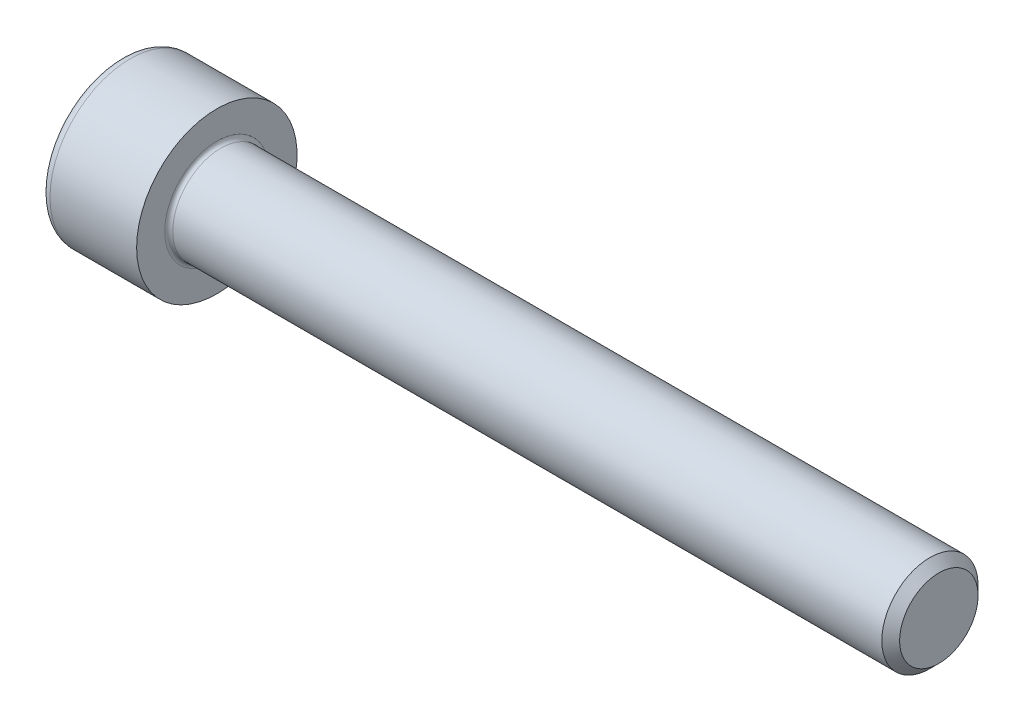
SolidWorks part; units mm, degrees
ref_plane "Plane1" through (0, 0, 0) normal (0, 0, 1) x (1, 0, 0)
ref_plane "Plane2" through (0, 0, 0) normal (0, 1, 0) x (1, 0, 0)
ref_plane "Plane3" through (0, 0, 0) normal (1, 0, 0) x (0, 0, -1)
sketch "BodySke" plane through (0, 0, 0) normal (0, 0, 1) x (1, 0, 0)
  line L0 (0, 0) -> (0, 5)
  line L1 (0, 5) -> (6, 5)
  line L2 (6, 5) -> (6, 3)
  line L3 (6, 3) -> (50.4455, 3)
  line L4 (51, 2.4455) -> (51, 0)
  line L5 (51, 0) -> (0, 0)
  line L6 (-31.75, 0) -> (127, 0) construction
  line L8 (51, 2.4455) -> (50.4455, 3)
  line L10 (51, -2.4455) -> (50.4455, -3) construction
  line L11 (7, 9.525) -> (7, 3.175) construction
  line L12 (27, 9.525) -> (27, 3.175) construction
  line L13 (-9, 9.525) -> (-9, 3.175) construction
  dimension "Diameter" = 6
  dimension "Head_ht" = 6
  dimension "Length" = 45
  dimension "Body_ch_ang" = 45
  dimension "Head_dia" = 10
  dimension "Minor_dia" = 4.891
  dimension "Advance" = 1
  dimension "Thread_nom" = 24
  dimension "Thread_length" = 60
revolve "Base-Revolve" add sketch "BodySke"
cosmetic thread "ThreadCosmetic" [suppressed]
fillet "Fillet1" radius 0.25 1 edges at (6, 0, 3)
fillet "Fillet2" radius 0.6 1 edges at (0, 0, 5)
sketch "Sketch2" plane through (0, 0, 0) normal (0, 0, 1) x (1, 0, 0)
  line L0 (0, 2.51) -> (3, 2.51)
  line L1 (3, 2.51) -> (4.4491, 0)
  line L2 (-31.75, 0) -> (127, 0) construction
  line L3 (4.4491, 0) -> (0, 0)
  line L4 (0, 0) -> (0, 2.51)
  line L6 (0, 0) -> (47.625, 0) construction
  dimension "D1" = 2.51
  dimension "D2" = 60
  dimension "Depth" = 3
revolve "Hex-PreBroach" cut sketch "Sketch2" angle 360 about L6
sketch "Sketch3" plane through (0, 0, 0) normal (-1, 0, 0) x (0, 0.5, 0.866)
  line L0 (1.4491, 2.51) -> (-1.4491, 2.51)
  line L1 (-1.4491, 2.51) -> (-2.8983, 0)
  line L2 (1.4491, 2.51) -> (2.8983, 0)
  line L3 (1.4491, -2.51) -> (2.8983, 0)
  line L4 (1.4491, -2.51) -> (-1.4491, -2.51)
  line L5 (-1.4491, -2.51) -> (-2.8983, 0)
  dimension "D1" = 2.51
  dimension "D2" = 2.51
  dimension "Hex_size" = 5.02
extrude "Hex" cut sketch "Sketch3" against normal blind 3
sketch "ThdSchSke" plane through (0, 0, 0) normal (0, 0, 1) x (1, 0, 0)
  line L0 (27, -2.4455) -> (26.6117, -3)
  line L1 (27, -2.4455) -> (27.3883, -3)
  line L2 (27.3883, -3) -> (27.3883, -3.75)
  line L3 (-3.175, 0) -> (5.1513, 0) construction
  line L4 (0, 4.4) -> (0, -4.4) construction
  line L5 (27.3883, -3.75) -> (26.6117, -3.75)
  line L6 (26.6117, -3.75) -> (26.6117, -3)
  dimension "Thread_minor" = 4.891
  dimension "Diameter" = 6
  dimension "Start" = 27
  dimension "SideAngle" = 55
  dimension "VeeAngle" = 70
  dimension "Overcut" = 7.5
revolve "ThreadSchematic" [suppressed] cut sketch "ThdSchSke" angle 360 about L3
pattern_linear "ThdSchPat" [suppressed]
equation "\"D2@Sketch3\" = \"Hex_size@Sketch3\" / 2"
equation "\"D1@Sketch3\" = \"Hex_size@Sketch3\" / 2"
equation "\"D1@Sketch2\" = \"Hex_size@Sketch3\" / 2"
equation "\"Thread_minor@ThreadCosmetic\"  =  \"Minor_dia@BodySke\""
equation "\"Depth@Sketch2\" =  \"Key_eng@Hex\""
equation "\"Thread_length@ThreadCosmetic\" = ((sgn( (\"Length@BodySke\" - \"Advance@BodySke\" * 3.0) - \"Thread_nom@BodySke\" )-1)*( (\"Length@BodySke\" - \"Advance@BodySke\" * 3.0) - \"Thread_nom@BodySke\" ))/-2+ \"Thread_nom@BodySke\""
equation "\"Thread_minor@ThdSchSke\" = \"Minor_dia@BodySke\""
equation "\"Diameter@ThdSchSke\" = \"Diameter@BodySke\""
equation "\"Overcut@ThdSchSke\" = \"Diameter@BodySke\" * 1.25"
equation "\"Start@ThdSchSke\" = \"Head_ht@BodySke\" + \"Length@BodySke\" - \"Thread_length@ThreadCosmetic\"  '---Non-countersunk---"
equation "\"Num_threads@ThdSchPat\" = int( \"Thread_length@ThreadCosmetic\" / \"Advance@BodySke\" + 0.999 )  + 1"
equation "\"Advance@ThdSchPat\" = \"Thread_length@ThreadCosmetic\" /  (\"Num_threads@ThdSchPat\" - 1) 'relax it"
equation "\"Num_threads@ThdSchPat\" = \"Num_threads@ThdSchPat\" - sgn( \"Num_threads@ThdSchPat\" - 1) '---chamfered tips only---"
